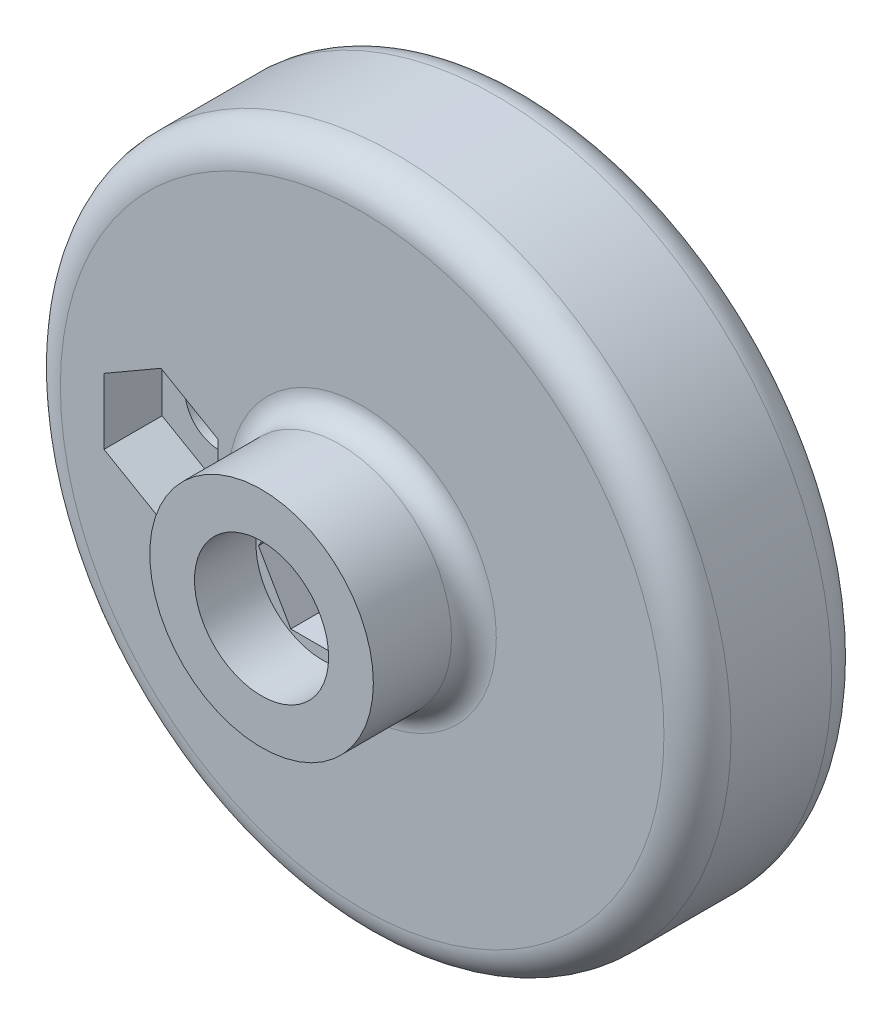
SolidWorks part; units mm, degrees
ref_plane "Front Plane" through (0, 0, 0) normal (0, 0, 1) x (1, 0, 0)
ref_plane "Top Plane" through (0, 0, 0) normal (0, 1, 0) x (1, 0, 0)
ref_plane "Right Plane" through (0, 0, 0) normal (1, 0, 0) x (0, 0, -1)
sketch "Sketch1" plane through (0, 0, 0) normal (0, 0, 1) x (1, 0, 0)
  circle A0 centre (0, 0) radius 30
  dimension "D1" = 60
extrude "Boss-Extrude1" add sketch "Sketch1" along normal blind 15
sketch "Sketch2" plane through (0, 0, 15) normal (0, 0, 1) x (1, 0, 0)
  circle A0 centre (0, 0) radius 10
  dimension "D1" = 20
extrude "Boss-Extrude2" add sketch "Sketch2" along normal blind 9
sketch "Sketch3" plane through (0, 0, 24) normal (0, 0, 1) x (1, 0, 0)
  circle A0 centre (0, 0) radius 3.25
  dimension "D1" = 6.5
extrude "Cut-Extrude1" cut sketch "Sketch3" against normal through all
fillet "Fillet1" radius 3 3 edges at (30, 0, 0) (30, 0, 15) (3.25, 0, 0)
hole_wizard "M5x0.8 Tapped Hole1" positions "Sketch6" profile "Sketch5" tap size "M5x0.8" standard "ANSI Metric"
sketch "Sketch6" plane through (0, 0, 0) normal (1, 0, 0) x (0, 0, -1)
  line L0 (-15, 10) -> (-15, -10) construction
  line L1 (-1000, 0) -> (49000, 0) construction
  point P0 (-19.5, 0)
  dimension "D1" = 4.5
sketch "Sketch5" plane through (0, 0, 19.5) normal (0, 1, 0) x (0, 0, 1)
  line L0 (0, 0) -> (0, 30)
  line L1 (0, 30) -> (2.1, 30)
  line L2 (2.1, 30) -> (2.1, 0)
  line L5 (2.1, 0) -> (0, 0)
  line L11 (0, -6.35) -> (0, 107.95) construction
  dimension "Thru Tap Drill Dia." = 4.2
  dimension "Thru Tap Drill Depth" = 30
cosmetic thread "Hole Thread1" [suppressed]
sketch "Sketch8" plane through (0, 0, 15) normal (0, 0, 1) x (1, 0, 0)
  line L0 (-1000, 0) -> (49000, 0) construction
  circle A0 centre (-18, 0) radius 3.05
  dimension "D1" = 6.1
  dimension "D2" = 18
extrude "Cut-Extrude3" cut sketch "Sketch8" against normal through all
sketch "Sketch7" plane through (0, 0, 15) normal (0, 0, 1) x (1, 0, 0)
  line L1 (-23.1, 2.9445) -> (-23.1, -2.9445)
  line L2 (-23.1, -2.9445) -> (-18, -5.889)
  line L3 (-18, -5.889) -> (-12.9, -2.9445)
  line L4 (-12.9, -2.9445) -> (-12.9, 2.9445)
  line L5 (-12.9, 2.9445) -> (-18, 5.889)
  line L6 (-18, 5.889) -> (-23.1, 2.9445)
  circle A0 centre (-18, 0) radius 5.1 construction
  circle A1 centre (-18, 0) radius 3.05 construction
  dimension "D1" = 10.2
extrude "Cut-Extrude4" cut sketch "Sketch7" against normal blind 5.2
sketch "Sketch9" plane through (0, 0, 24) normal (0, 0, 1) x (1, 0, 0)
  circle A0 centre (0, 0) radius 6
  dimension "D1" = 12
extrude "Cut-Extrude5" cut sketch "Sketch9" against normal blind 5.5
sketch "Sketch10" plane through (0, 0, 18.5) normal (0, 0, 1) x (1, 0, 0)
  line L1 (5.7735, 0) -> (2.8868, 5)
  line L2 (2.8868, 5) -> (-2.8868, 5)
  line L3 (-2.8868, 5) -> (-5.7735, 0)
  line L4 (-5.7735, 0) -> (-2.8868, -5)
  line L5 (-2.8868, -5) -> (2.8868, -5)
  line L6 (2.8868, -5) -> (5.7735, 0)
  circle A0 centre (0, 0) radius 5 construction
  dimension "D1" = 10
extrude "Cut-Extrude6" cut sketch "Sketch10" against normal blind 5.5
fillet "Fillet2" radius 2 1 edges at (10, 0, 15)
